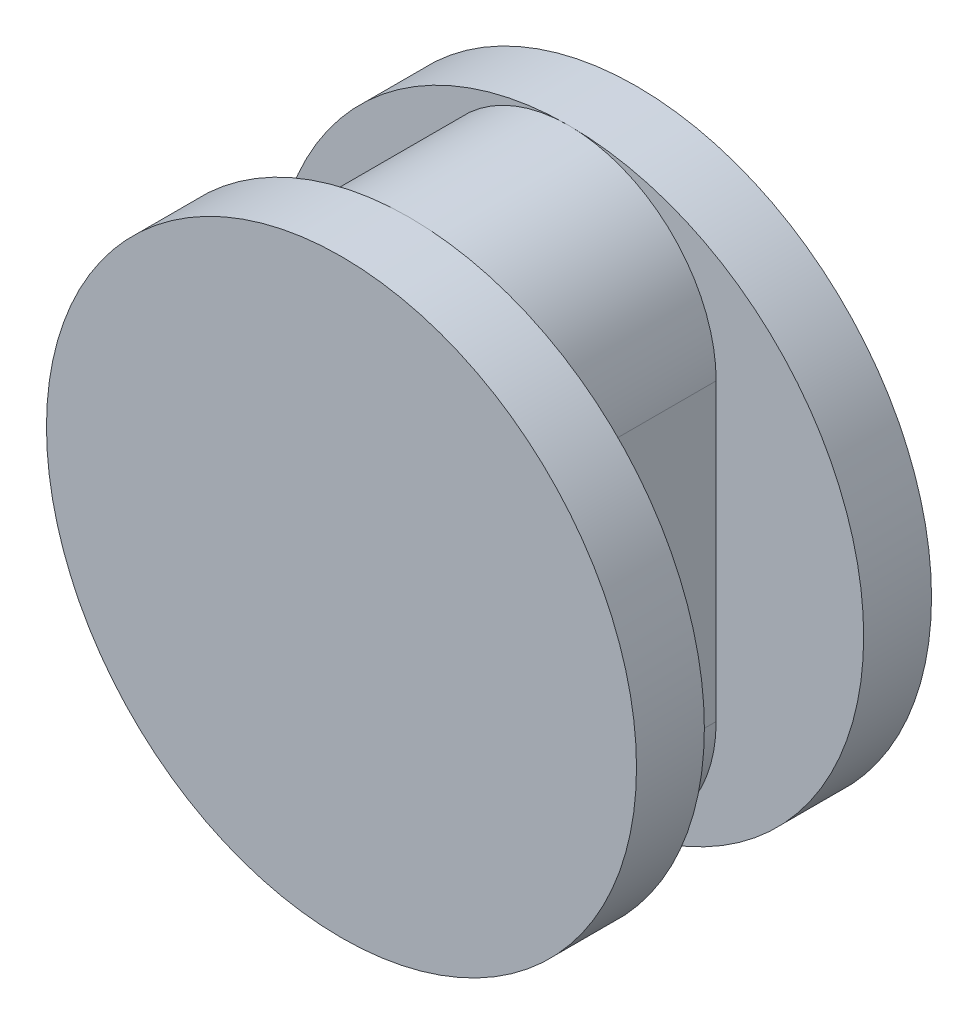
SolidWorks part; units mm, degrees
material "6061-T6 (SS)"
ref_plane "Płaszczyzna przednia" through (0, 0, 0) normal (0, 0, 1) x (1, 0, 0)
ref_plane "Płaszczyzna górna" through (0, 0, 0) normal (0, 1, 0) x (1, 0, 0)
ref_plane "Płaszczyzna prawa" through (0, 0, 0) normal (1, 0, 0) x (0, 0, -1)
sketch "Szkic1" plane through (0, 0, 0) normal (0, 0, 1) x (1, 0, 0)
  line L0 (5, -10) -> (5, 0)
  line L1 (-5, 0) -> (-5, -10)
  arc A0 (-5, -10) -> (5, -10) centre (0, -10) ccw
  arc A1 (5, 0) -> (-5, 0) centre (0, 0) ccw
  dimension "D1" = 10
  dimension "D2" = 10
  dimension "D3" = 10
extrude "Dodanie-wyciągnięcie1" add sketch "Szkic1" along normal mid plane 5.4
sketch "Szkic2" plane through (0, 0, 2.7) normal (0, 0, 1) x (1, 0, 0)
  line L2 (5, -10) -> (5, 0)
  line L3 (-5, 0) -> (-5, -10)
  line L4 (5, -10) -> (5, 0)
  line L5 (-5, 0) -> (-5, -10)
  circle A0 centre (0, -5) radius 10
  arc A2 (-5, -10) -> (5, -10) centre (0, -10) ccw
  arc A3 (5, 0) -> (-5, 0) centre (0, 0) ccw
  arc A4 (-5, -10) -> (5, -10) centre (0, -10) ccw
  arc A5 (5, 0) -> (-5, 0) centre (0, 0) ccw
  dimension "D2" = 20
  dimension "D1" = 0
extrude "Dodanie-wyciągnięcie2" add sketch "Szkic2" along normal blind 2.3 contours A0
sketch "Szkic3" plane through (0, 0, -2.7) normal (0, 0, -1) x (-1, 0, 0)
  line L2 (5, -10) -> (5, 0)
  line L3 (-5, 0) -> (-5, -10)
  line L4 (5, -10) -> (5, 0)
  line L5 (-5, 0) -> (-5, -10)
  circle A0 centre (0, -5) radius 10
  arc A2 (-5, -10) -> (5, -10) centre (0, -10) ccw
  arc A3 (5, 0) -> (-5, 0) centre (0, 0) ccw
  arc A4 (-5, -10) -> (5, -10) centre (0, -10) ccw
  arc A5 (5, 0) -> (-5, 0) centre (0, 0) ccw
  arc M5 (-5, -10) -> (5, -10) centre (0, -10) ccw
  line M6 (5, -10) -> (5, 0)
  arc M7 (5, 0) -> (-5, 0) centre (0, 0) ccw
  line M8 (-5, 0) -> (-5, -10)
  dimension "D2" = 20
  dimension "D1" = 0
extrude "Dodanie-wyciągnięcie3" add sketch "Szkic3" along normal blind 2.3 contours A0 M5 M7 M6 | M8 M5 M6 M7 | A0 M7 M5 M8
ref_plane "Płaszczyzna symetrii" through (0, 0, 0) normal (0, 0, -1) x (-1, 0, 0)
